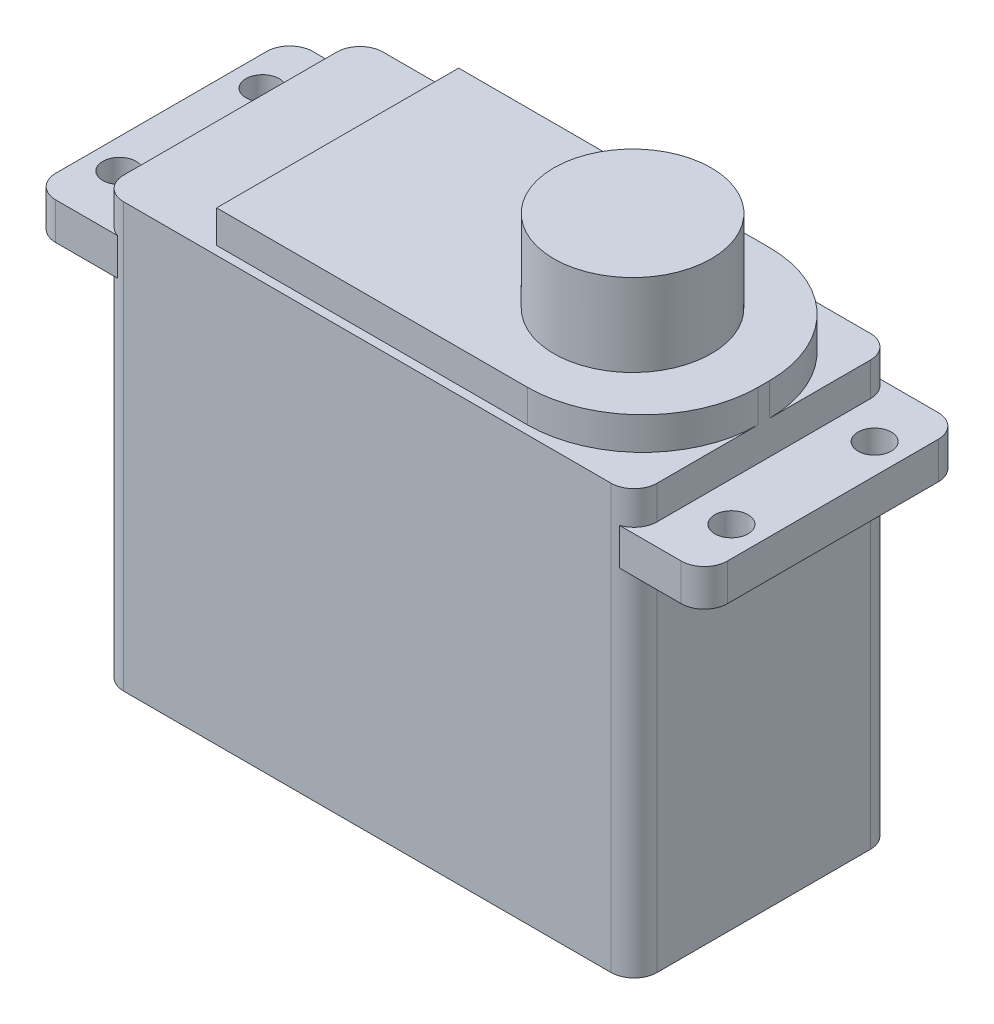
SolidWorks part; units mm, degrees
ref_plane "Front" through (0, 0, 0) normal (0, 0, 1) x (1, 0, 0)
ref_plane "Top" through (0, 0, 0) normal (0, 1, 0) x (1, 0, 0)
ref_plane "Right" through (0, 0, 0) normal (1, 0, 0) x (0, 0, -1)
sketch "Sketch1" plane through (0, 0, 0) normal (0, 1, 0) x (1, 0, 0)
  line L1 (29.337, -14.2621) -> (-29.337, -14.2621)
  line L2 (29.337, -14.2621) -> (29.337, 14.2621)
  line L3 (29.337, 14.2621) -> (-29.337, 14.2621)
  line L4 (-29.337, -14.2621) -> (-29.337, 14.2621)
  line L5 (29.337, -14.2621) -> (-29.337, 14.2621) construction
  line L6 (29.337, 14.2621) -> (-29.337, -14.2621) construction
  point P0 (0, 0)
  dimension "D1" = 28.5242
  dimension "D2" = 58.674
extrude "Boss-Extrude1" add sketch "Sketch1" along normal blind 46.609
sketch "Sketch2" plane through (0, 46.609, 0) normal (0, 1, 0) x (1, 0, 0)
  line L0 (-29.337, 0) -> (-17.526, 0) construction
  line L1 (-29.337, 14.2621) -> (-29.337, -14.2621) construction
  line L2 (29.337, -14.2621) -> (29.337, 14.2621) construction
  line L3 (29.337, -13.3096) -> (29.337, 13.3096)
  line L4 (-17.526, 0) -> (29.337, 0) construction
  line L5 (29.337, 13.3096) -> (-17.526, 13.3096)
  line L6 (-17.526, -13.3096) -> (-17.526, 13.3096)
  line L7 (29.337, -13.3096) -> (-17.526, -13.3096)
  dimension "D1" = 13.3096
  dimension "D2" = 11.811
extrude "Boss-Extrude2" add sketch "Sketch2" along normal blind 3.5814
fillet "Fillet1" radius 12.7 2 edges
fillet "Fillet2" radius 2.54 4 edges at (29.337, 23.3045, 14.2621) (29.337, 23.3045, -14.2621) (-29.337, 23.3045, -14.2621) (-29.337, 23.3045, 14.2621)
sketch "Sketch3" plane through (0, 46.609, 0) normal (0, 1, 0) x (1, 0, 0)
  line L0 (26.797, 14.2621) -> (-26.797, 14.2621) construction
  line L1 (36.9316, -14.1351) -> (-36.9316, -14.1351)
  line L2 (36.9316, -14.1351) -> (36.9316, 14.1351)
  line L3 (36.9316, 14.1351) -> (-36.9316, 14.1351)
  line L4 (-36.9316, -14.1351) -> (-36.9316, 14.1351)
  line L5 (36.9316, -14.1351) -> (-36.9316, 14.1351) construction
  line L6 (36.9316, 14.1351) -> (-36.9316, -14.1351) construction
  line L7 (0, 14.1351) -> (0, -14.1351) construction
  point P0 (0, 0)
  dimension "D1" = 0.127
  dimension "D2" = 73.8632
extrude "Boss-Extrude3" add sketch "Sketch3" along normal blind 4.064 from offset 7.747 offset against normal yes
fillet "Fillet3" radius 2.54 4 edges at (-36.9316, 40.894, -14.1351) (-36.9316, 40.894, 14.1351) (36.9316, 40.894, 14.1351) (36.9316, 40.894, -14.1351)
sketch "Sketch4" plane through (0, 42.926, 0) normal (0, 1, 0) x (1, 0, 0)
  line L5 (33.655, -7.874) -> (-33.655, 7.874) construction
  line L6 (33.655, 7.874) -> (-33.655, -7.874) construction
  circle A0 centre (-33.655, 7.874) radius 1.8288
  circle A1 centre (-33.655, -7.874) radius 1.8288
  circle A2 centre (33.655, -7.874) radius 1.8288
  circle A3 centre (33.655, 7.874) radius 1.8288
  point P0 (0, 0)
  dimension "D3" = 3.6576
  dimension "D4" = 3.6576
  dimension "D5" = 3.6576
  dimension "D6" = 3.6576
  dimension "D1" = 15.748
  dimension "D2" = 67.31
extrude "Cut-Extrude1" cut sketch "Sketch4" against normal through all
sketch "Sketch5" plane through (0, 46.609, 0) normal (0, 1, 0) x (1, 0, 0)
  line L0 (-29.337, 0) -> (29.337, 0) construction
  line L1 (-29.337, 11.7221) -> (-29.337, -11.7221) construction
  line L2 (29.337, -0.6096) -> (29.337, 0.6096) construction
  line L3 (29.337, 0) -> (29.337, 14.1351) construction
  line L4 (34.3916, 14.1351) -> (27.5901, 14.1351) construction
  line L5 (29.337, 14.1351) -> (14.9098, 14.2621) construction
  line L6 (26.797, 14.2621) -> (-26.797, 14.2621) construction
  line L7 (14.9098, 14.2621) -> (14.9098, -14.2621) construction
  line L8 (-26.797, -14.2621) -> (26.797, -14.2621) construction
  circle A0 centre (14.9098, 0) radius 8.6614
  dimension "D2" = 17.3228
  dimension "D1" = 14.4272
extrude "Boss-Extrude4" add sketch "Sketch5" along normal blind 12.6238
